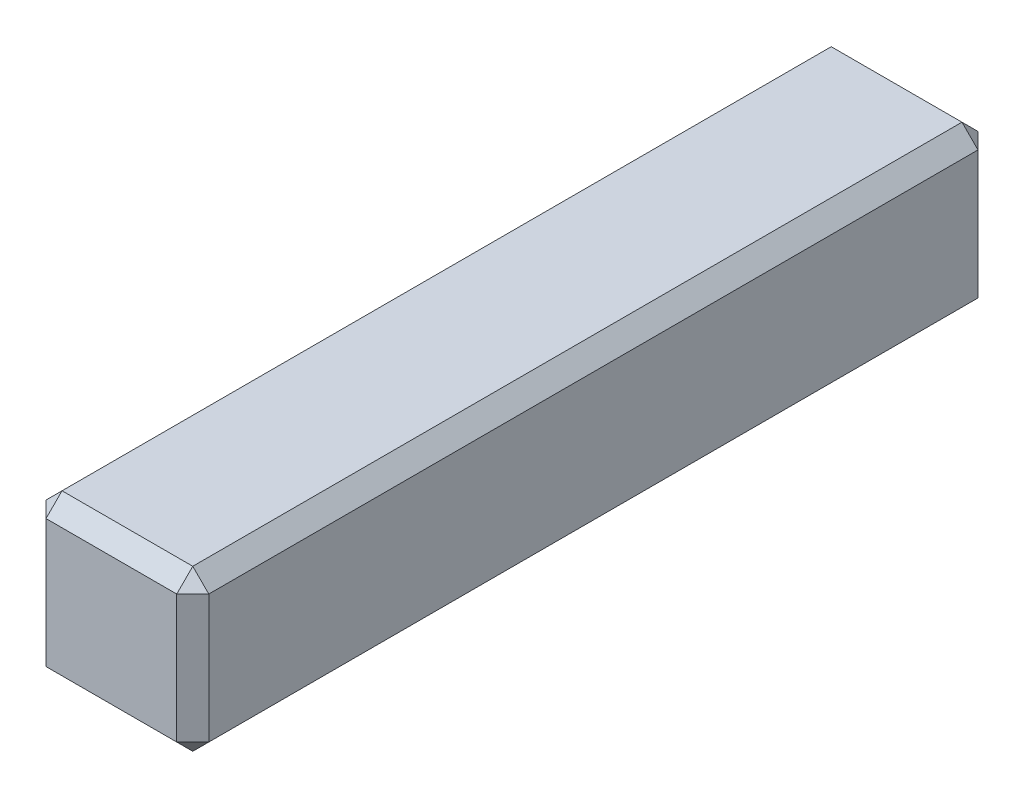
SolidWorks part; units mm, degrees
ref_plane "Front Plane" through (0, 0, 0) normal (0, 0, 1) x (1, 0, 0)
ref_plane "Top Plane" through (0, 0, 0) normal (0, 1, 0) x (1, 0, 0)
ref_plane "Right Plane" through (0, 0, 0) normal (1, 0, 0) x (0, 0, -1)
sketch "Sketch1" plane through (0, 0, 0) normal (0, 0, 1) x (1, 0, 0)
  line L0 (-51.221, 13.5531) -> (-51.221, 11.5531) construction
  line L1 (-49.1893, 13.5531) -> (-51.221, 13.5531)
  line L2 (-49.1893, 13.5531) -> (-49.1893, 11.5531)
  line L3 (-49.1893, 11.5531) -> (-51.221, 11.5531)
  line L4 (-51.221, 13.5531) -> (-51.221, 11.5531)
  line L5 (-51.221, 11.5531) -> (-50.1893, 11.5531) construction
extrude "Boss-Extrude1" add sketch "Sketch1" along normal mid plane 10 contours L2 L3 L4 L1
chamfer "Chamfer1" distance 0.2 angle 45 12 edges at (-50.2051, 11.5531, 5) (-50.2051, 13.5531, -5) (-49.1893, 12.5531, -5) (-50.2051, 11.5531, -5) (-51.221, 12.5531, -5) (-51.221, 11.5531, 0) (-51.221, 12.5531, 5) (-49.1893, 11.5531, 0) (-49.1893, 12.5531, 5) (-49.1893, 13.5531, 0) (-50.2051, 13.5531, 5) (-51.221, 13.5531, 0)
